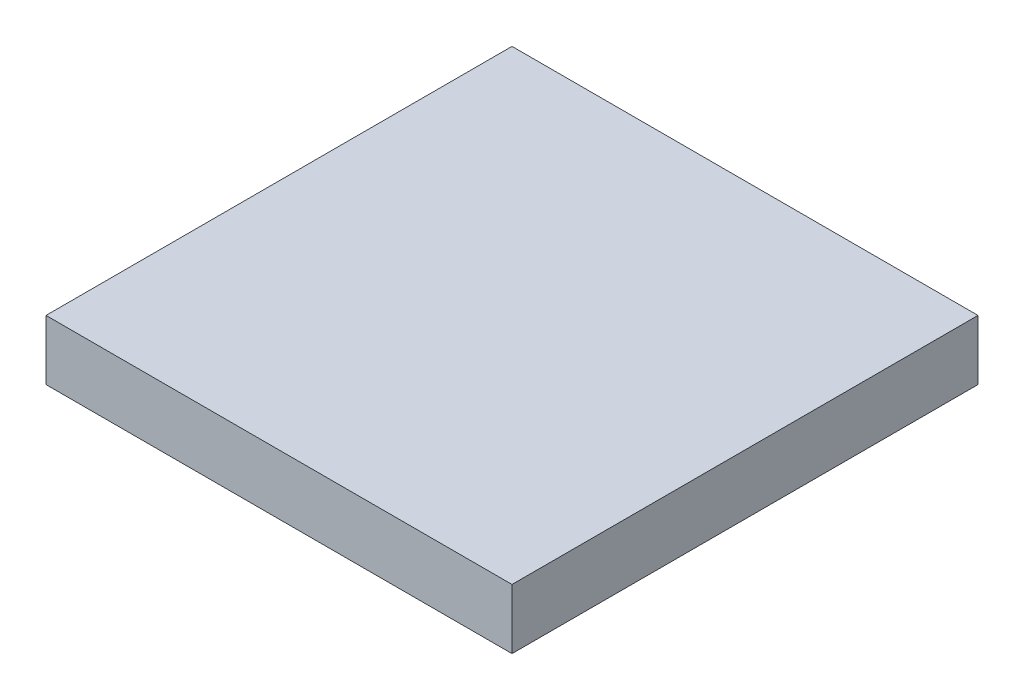
SolidWorks part; units mm, degrees
ref_plane "Front Plane" through (0, 0, 0) normal (0, 0, 1) x (1, 0, 0)
ref_plane "Top Plane" through (0, 0, 0) normal (0, 1, 0) x (1, 0, 0)
ref_plane "Right Plane" through (0, 0, 0) normal (1, 0, 0) x (0, 0, -1)
sketch "BaseS" plane through (0, 0, 0) normal (0, 1, 0) x (1, 0, 0)
  line L1 (-3.5, 3.5) -> (3.5, 3.5)
  line L2 (-3.5, 3.5) -> (-3.5, -3.5)
  line L3 (-3.5, -3.5) -> (3.5, -3.5)
  line L4 (3.5, 3.5) -> (3.5, -3.5)
  line L5 (-3.5, 3.5) -> (3.5, -3.5) construction
  line L6 (-3.5, -3.5) -> (3.5, 3.5) construction
  point P0 (0, 0)
  dimension "Dim" = 7
extrude "Base" add sketch "BaseS" along normal blind 0.9
